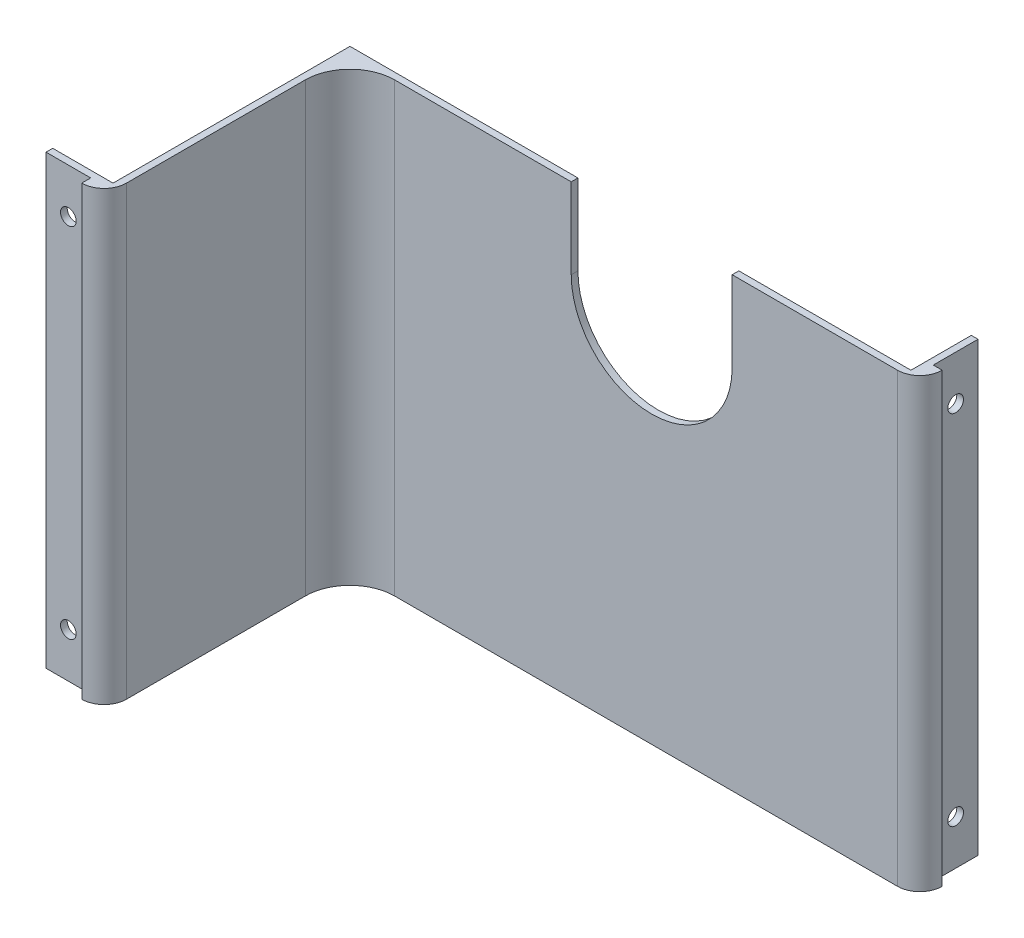
SolidWorks part; units mm, degrees
material "ABS"
ref_plane "Спереди" through (0, 0, 0) normal (0, 0, 1) x (1, 0, 0)
ref_plane "Сверху" through (0, 0, 0) normal (0, 1, 0) x (1, 0, 0)
ref_plane "Справа" through (0, 0, 0) normal (1, 0, 0) x (0, 0, -1)
sketch "Эскиз1" plane through (0, 0, 0) normal (0, 1, 0) x (1, 0, 0)
  line L0 (0, 0) -> (-112.5, 0)
  line L1 (-122.5, -10) -> (-122.5, -50)
  line L2 (-127.5, -55) -> (-127.5, -53)
  line L3 (-127.5, -53) -> (-137.5, -53)
  line L4 (5, 5) -> (3, 5)
  line L5 (3, 5) -> (3, 15)
  line L6 (3, 15) -> (1.5, 15)
  line L7 (0, 0) -> (0, 1.5) construction
  line L8 (1.5, 15) -> (1.5, 1.5)
  line L9 (-122.5, -50) -> (-124, -50) construction
  line L10 (-137.5, -53) -> (-137.5, -51.5)
  line L11 (-137.5, -51.5) -> (-124, -51.5)
  line L12 (-124, -51.5) -> (-124, 1.5)
  line L13 (-124, 1.5) -> (1.5, 1.5)
  arc A0 (-112.5, 0) -> (-122.5, -10) centre (-112.5, -10) ccw
  arc A1 (-122.5, -50) -> (-127.5, -55) centre (-127.5, -50) cw
  arc A2 (0, 0) -> (5, 5) centre (0, 5) ccw
  dimension "D1" = 112.5
  dimension "D2" = 5
  dimension "D6" = 10
  dimension "D9" = 5
  dimension "D3" = 2
  dimension "D4" = 1.5
  dimension "D5" = 1.5
  dimension "D7" = 1.5
  dimension "D8" = 40
  dimension "D10" = 2
  dimension "D11" = 1.5
  dimension "D12" = 10
  dimension "D13" = 10
extrude "Бобышка-Вытянуть1" add sketch "Эскиз1" along normal blind 100
sketch "Эскиз2" plane through (0, 0, 0) normal (0, 0, 1) x (1, 0, 0)
  line L8 (-73, 100) -> (-37, 100)
  line L9 (-73, 82) -> (-73, 100)
  line L10 (-37, 100) -> (-37, 82)
  line L11 (5, 100) -> (-37, 100) construction
  arc A1 (-73, 82) -> (-37, 82) centre (-55, 82) ccw
  dimension "D4" = 18
  dimension "D1" = 42
  dimension "D2" = 36
  dimension "D3" = 18
extrude "Вырез-Вытянуть1" cut sketch "Эскиз2" against normal blind 10
sketch "Эскиз3" plane through (3, 0, 0) normal (1, 0, 0) x (0, 0, -1)
  line L0 (10, 100) -> (10, 0) construction
  line L1 (5, 100) -> (15, 100) construction
  line L2 (5, 0) -> (15, 0) construction
  line L3 (15, 50) -> (5, 50) construction
  line L4 (15, 100) -> (15, 0) construction
  line L5 (5, 100) -> (5, 0) construction
  circle A0 centre (10, 90) radius 1.75
  circle A1 centre (10, 10) radius 1.75
  dimension "D1" = 3.5
  dimension "D2" = 10
extrude "Вырез-Вытянуть2" cut sketch "Эскиз3" against normal blind 10
sketch "Эскиз4" plane through (0, 0, 53) normal (0, 0, 1) x (1, 0, 0)
  line L0 (-132.5, 100) -> (-132.5, 0) construction
  line L1 (-137.5, 100) -> (-127.5, 100) construction
  line L2 (-137.5, 0) -> (-127.5, 0) construction
  line L3 (-137.5, 50) -> (-127.5, 50) construction
  line L4 (-137.5, 100) -> (-137.5, 0) construction
  line L5 (-127.5, 100) -> (-127.5, 0) construction
  circle A0 centre (-132.5, 90) radius 1.75
  circle A1 centre (-132.5, 10) radius 1.75
  dimension "D1" = 3.5
  dimension "D2" = 10
extrude "Вырез-Вытянуть3" cut sketch "Эскиз4" against normal blind 10
